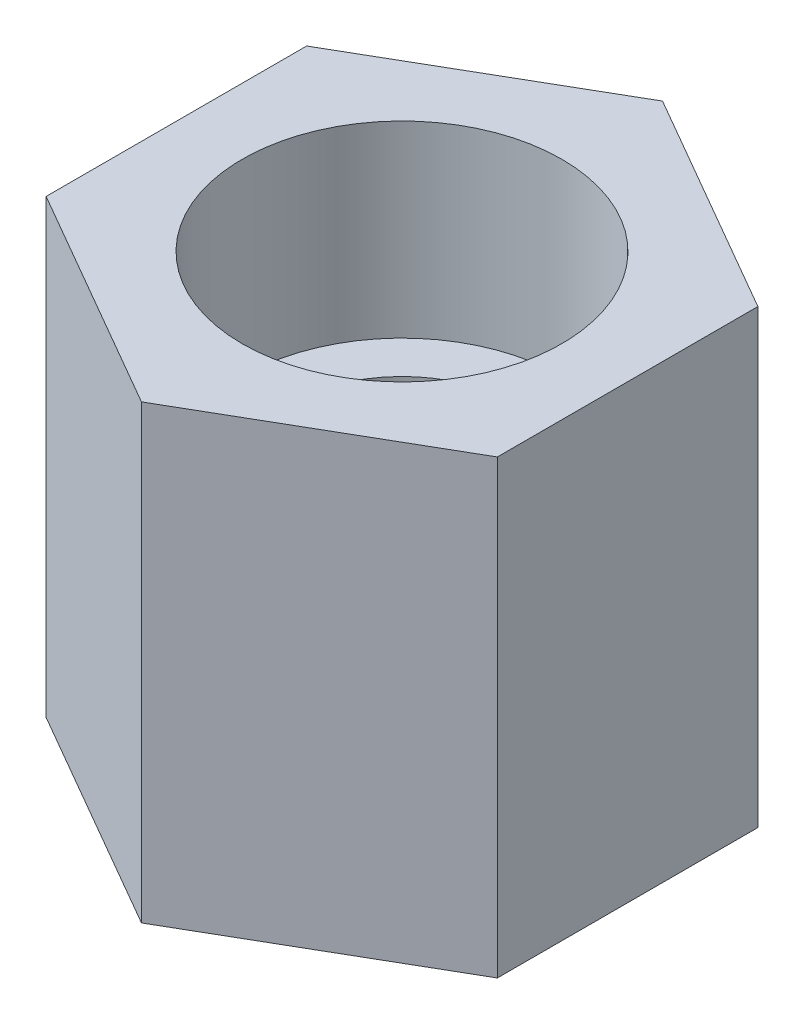
SolidWorks part; units mm, degrees
ref_plane "Спереди" through (0, 0, 0) normal (0, 0, 1) x (1, 0, 0)
ref_plane "Сверху" through (0, 0, 0) normal (0, 1, 0) x (1, 0, 0)
ref_plane "Справа" through (0, 0, 0) normal (1, 0, 0) x (0, 0, -1)
sketch "Эскиз1" plane through (0, 0, 0) normal (0, 1, 0) x (1, 0, 0)
  line L1 (0, 13.8564) -> (-12, 6.9282)
  line L2 (-12, 6.9282) -> (-12, -6.9282)
  line L3 (-12, -6.9282) -> (0, -13.8564)
  line L4 (0, -13.8564) -> (12, -6.9282)
  line L5 (12, -6.9282) -> (12, 6.9282)
  line L6 (12, 6.9282) -> (0, 13.8564)
  circle A0 centre (0, 0) radius 12 construction
  circle A1 centre (0, 0) radius 6
extrude "Бобышка-Вытянуть1" add sketch "Эскиз1" along normal blind 24
sketch "Эскиз3" plane through (0, 24, 0) normal (0, 1, 0) x (1, 0, 0)
  circle A0 centre (0, 0) radius 8.5
extrude "Вырез-Вытянуть2" cut sketch "Эскиз3" against normal blind 10
